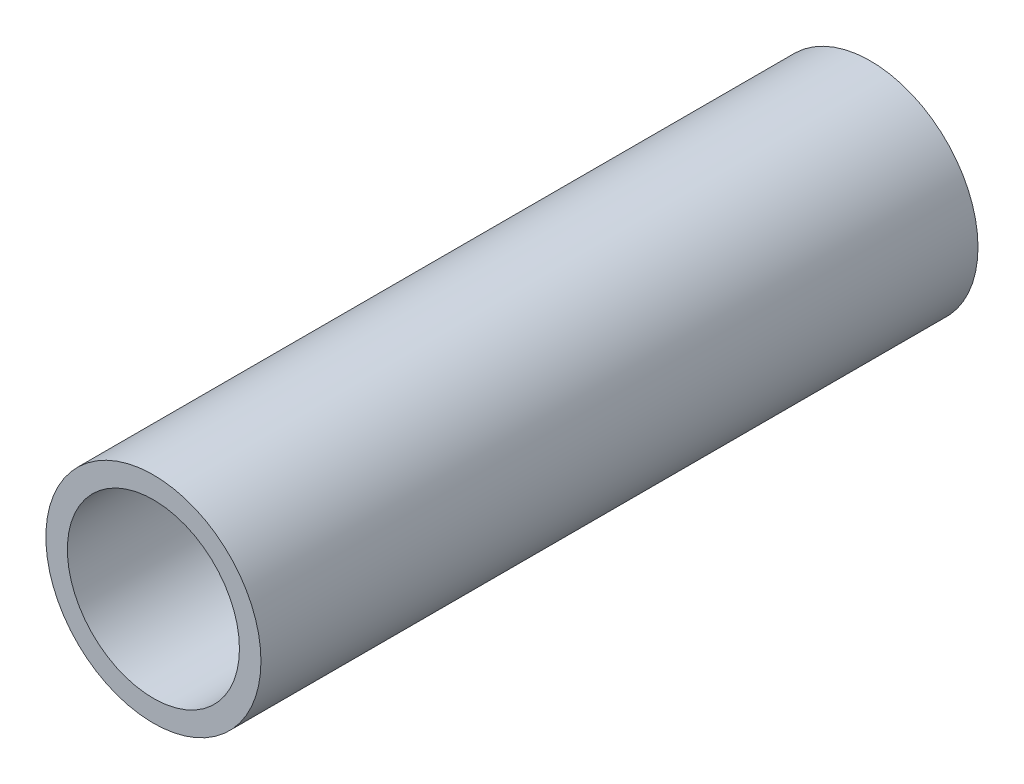
SolidWorks part; units mm, degrees
ref_plane "Front Plane" through (0, 0, 0) normal (0, 0, 1) x (1, 0, 0)
ref_plane "Top Plane" through (0, 0, 0) normal (0, 1, 0) x (1, 0, 0)
ref_plane "Right Plane" through (0, 0, 0) normal (1, 0, 0) x (0, 0, -1)
sketch "Sketch1" plane through (0, 0, 0) normal (0, 0, 1) x (1, 0, 0)
  circle A0 centre (0, 0) radius 7.5
  circle A1 centre (0, 0) radius 6
  dimension "D1" = 15
  dimension "D2" = 12
extrude "Boss-Extrude1" add sketch "Sketch1" along normal blind 50
